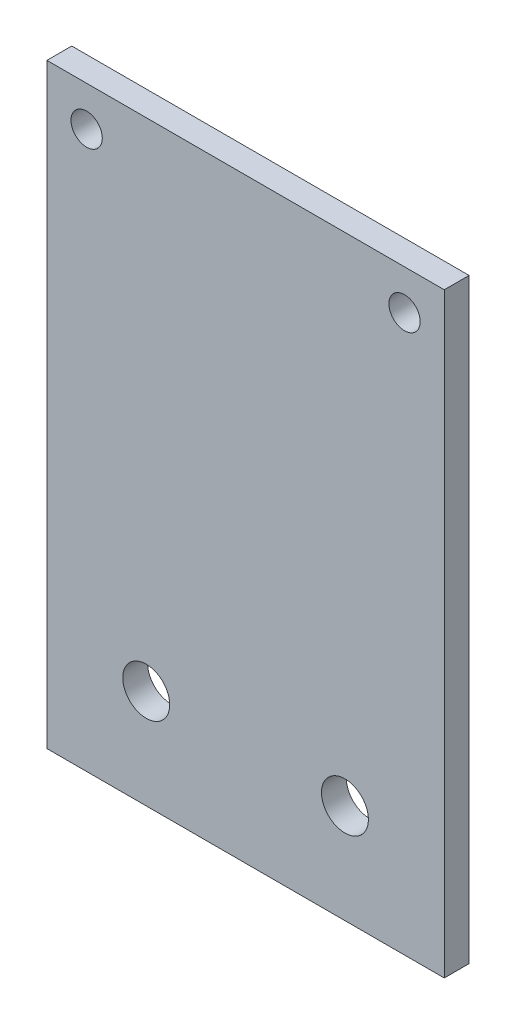
SolidWorks part; units mm, degrees
ref_plane "Front Plane" through (0, 0, 0) normal (0, 0, 1) x (1, 0, 0)
ref_plane "Top Plane" through (0, 0, 0) normal (0, 1, 0) x (1, 0, 0)
ref_plane "Right Plane" through (0, 0, 0) normal (1, 0, 0) x (0, 0, -1)
sketch "Sketch1" plane through (0, 0, 0) normal (0, 0, 1) x (1, 0, 0)
  line L1 (0, 0) -> (50.8, 0)
  line L2 (0, 0) -> (0, 76.2)
  line L3 (0, 76.2) -> (50.8, 76.2)
  line L4 (50.8, 0) -> (50.8, 76.2)
  dimension "D1" = 50.8
  dimension "D2" = 76.2
extrude "Boss-Extrude1" add sketch "Sketch1" along normal blind 3.175
sketch "Sketch2" plane through (0, 0, 3.175) normal (0, 0, 1) x (1, 0, 0)
  line L0 (50.8, 0) -> (50.8, 76.2) construction
  line L1 (0, 76.2) -> (0, 0) construction
  line L2 (50.8, 76.2) -> (0, 76.2) construction
  line L3 (0, 0) -> (50.8, 0) construction
  circle A0 centre (5.08, 71.12) radius 2
  circle A1 centre (45.72, 71.12) radius 2
  circle A2 centre (12.7, 12.7) radius 3
  circle A3 centre (38.1, 12.7) radius 3
  point P14 (25.4, 0)
  dimension "D1" = 4
  dimension "D2" = 5.08
  dimension "D6" = 6
  dimension "D7" = 25.4
  dimension "D3" = 5.08
  dimension "D4" = 5.08
  dimension "D5" = 5.08
  dimension "D8" = 12.7
  dimension "D9" = 12.7
extrude "Cut-Extrude1" cut sketch "Sketch2" against normal through all
equation "\"D3@Sketch2\" = \"D2@Sketch2\""
equation "\"D5@Sketch2\" = \"D4@Sketch2\""
